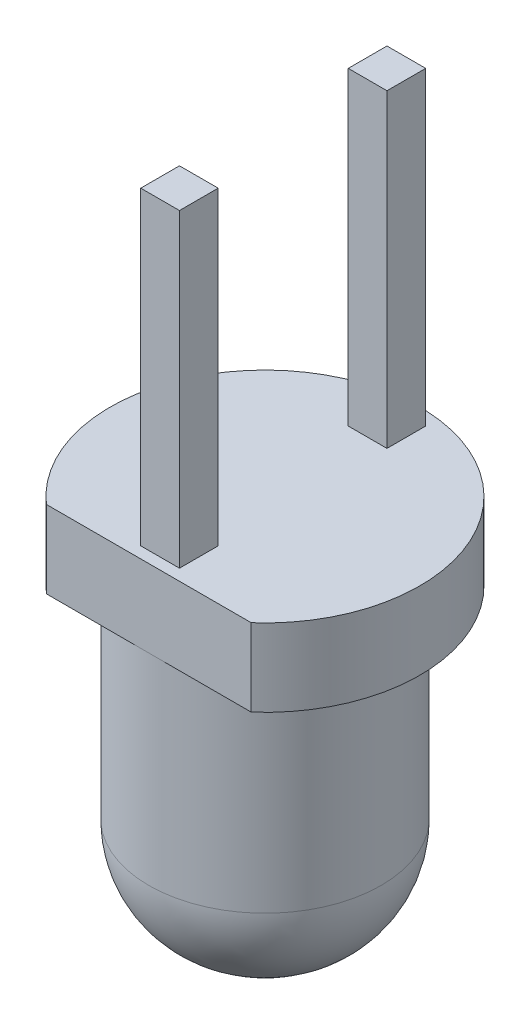
SolidWorks part; units mm, degrees
ref_plane "Спереди" through (0, 0, 0) normal (0, 0, 1) x (1, 0, 0)
ref_plane "Сверху" through (0, 0, 0) normal (0, 1, 0) x (1, 0, 0)
ref_plane "Справа" through (0, 0, 0) normal (1, 0, 0) x (0, 0, -1)
sketch "Эскиз1" plane through (0, 0, 0) normal (0, 1, 0) x (1, 0, 0)
  circle A0 centre (0, 0) radius 2
extrude "Бобышка-Вытянуть1" add sketch "Эскиз1" along normal blind 1
sketch "Эскиз2" plane through (0, 0, 0) normal (0, -1, 0) x (-1, 0, 0)
  circle A0 centre (0, 0) radius 1.5
extrude "Бобышка-Вытянуть2" add sketch "Эскиз2" along normal blind 4
fillet "Скругление1" radius 1.4 1 edges at (0, -4, -1.5)
sketch "Эскиз3" plane through (0, 0, 0) normal (0, -1, 0) x (1, 0, 0)
  line L1 (-1.3229, 1.5) -> (1.3229, 1.5)
  circle A1 centre (0, 0) radius 2 construction
  arc A2 (-1.3229, 1.5) -> (1.3229, 1.5) centre (0, 0) cw
extrude "Вырез-Вытянуть1" cut sketch "Эскиз3" against normal blind 4
sketch "Эскиз4" plane through (0, 1, 0) normal (0, 1, 0) x (1, 0, 0)
  line L0 (-0.25, -0.8539) -> (0.25, -0.8539)
  line L1 (-0.25, -0.8539) -> (-0.25, -1.3539)
  line L2 (0.25, -0.8539) -> (0.25, -1.3539)
  line L3 (-0.25, -1.3539) -> (0.25, -1.3539)
  line L4 (-0.25, -0.8539) -> (0.25, -1.3539) construction
  line L5 (0.25, -0.8539) -> (-0.25, -1.3539) construction
  line L6 (-0.25, 1.8255) -> (0.25, 1.8255)
  line L7 (-0.25, 1.8255) -> (-0.25, 1.3255)
  line L8 (0.25, 1.8255) -> (0.25, 1.3255)
  line L9 (-0.25, 1.3255) -> (0.25, 1.3255)
  line L10 (-0.25, 1.8255) -> (0.25, 1.3255) construction
  line L11 (0.25, 1.8255) -> (-0.25, 1.3255) construction
  point P1 (0, -1.1039)
  point P2 (0, 1.5755)
extrude "Бобышка-Вытянуть3" add sketch "Эскиз4" along normal blind 4
